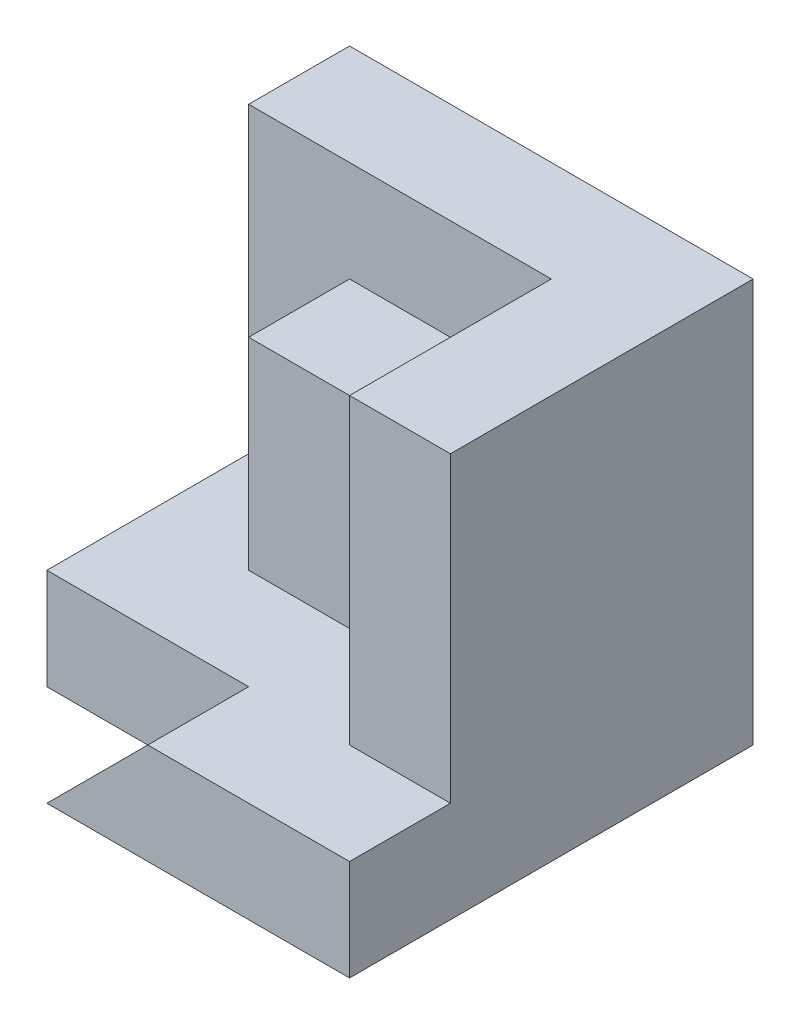
SolidWorks part; units mm, degrees
ref_plane "Front Plane" through (0, 0, 0) normal (0, 0, 1) x (1, 0, 0)
ref_plane "Top Plane" through (0, 0, 0) normal (0, 1, 0) x (1, 0, 0)
ref_plane "Right Plane" through (0, 0, 0) normal (1, 0, 0) x (0, 0, -1)
sketch "Sketch1" plane through (0, 0, 0) normal (0, 0, 1) x (1, 0, 0)
  line L1 (0, 0) -> (40, 0)
  line L2 (0, 0) -> (0, 40)
  line L3 (0, 40) -> (40, 40)
  line L4 (40, 0) -> (40, 40)
  dimension "D1" = 40
  dimension "D2" = 40
extrude "Boss-Extrude1" add sketch "Sketch1" along normal blind 40
sketch "Sketch2" plane through (0, 40, 0) normal (0, 1, 0) x (1, 0, 0)
  line L1 (0, -40) -> (10, -40)
  line L2 (0, -40) -> (0, -30)
  line L3 (0, -30) -> (10, -30)
  line L4 (10, -40) -> (10, -30)
  dimension "D1" = 10
  dimension "D2" = 10
extrude "Cut-Extrude1" cut sketch "Sketch2" against normal blind 40
sketch "Sketch4" plane through (10, 0, 0) normal (-1, 0, 0) x (0, 0, 1)
  line L1 (30, 40) -> (40, 40)
  line L2 (30, 40) -> (30, 0)
  line L3 (30, 0) -> (40, 0)
  line L4 (40, 40) -> (40, 0)
  line L5 (30, 40) -> (40, 40)
  line L6 (30, 40) -> (30, 10)
  line L7 (30, 10) -> (40, 10)
  line L8 (40, 40) -> (40, 10)
  line M5 (40, 40) -> (30, 40)
  line M6 (30, 40) -> (30, 0)
  dimension "D1" = 10
extrude "Cut-Extrude3" cut sketch "Sketch4" against normal blind 40 contours L7 L4 M6 M5
sketch "Sketch5" plane through (0, 0, 40) normal (0, 0, 1) x (1, 0, 0)
  line L0 (10, 0) -> (20, 10)
  line L1 (40, 10) -> (10, 10) construction
  line L2 (20, 10) -> (10, 10)
  line L3 (10, 10) -> (10, 0)
  dimension "D1" = 10
extrude "Cut-Extrude4" cut sketch "Sketch5" against normal blind 10
sketch "Sketch6" plane through (0, 40, 0) normal (0, 1, 0) x (1, 0, 0)
  line L0 (20, -30) -> (30, -30)
  line L1 (40, -30) -> (0, -30) construction
  line L2 (30, -30) -> (30, -20)
  line L3 (30, -20) -> (10, -20)
  line L4 (10, -20) -> (10, -10)
  line L5 (10, -10) -> (0, -10)
  line L6 (0, -30) -> (0, 0) construction
  line L7 (0, -10) -> (0, -30)
  line L8 (20, -30) -> (30, -30)
  line L9 (0, -30) -> (20, -30)
  line L10 (0, -30) -> (20, -30)
  line M1 (0, -30) -> (40, -30)
  line M4 (0, 0) -> (0, -30)
  dimension "D1" = 10
  dimension "D2" = 10
  dimension "D3" = 10
  dimension "D4" = 20
  dimension "D5" = 10
extrude "Cut-Extrude5" cut sketch "Sketch6" against normal blind 30 contours L4 L5 L2 L3 M4 M1
sketch "Sketch7" plane through (0, 0, 20) normal (0, 0, 1) x (1, 0, 0)
  line L0 (30, 10) -> (30, 40) construction
  line L1 (10, 40) -> (30, 40)
  line L2 (10, 40) -> (10, 30)
  line L3 (10, 30) -> (30, 30)
  line L4 (30, 40) -> (30, 30)
  dimension "D1" = 10
extrude "Cut-Extrude6" cut sketch "Sketch7" against normal blind 10
